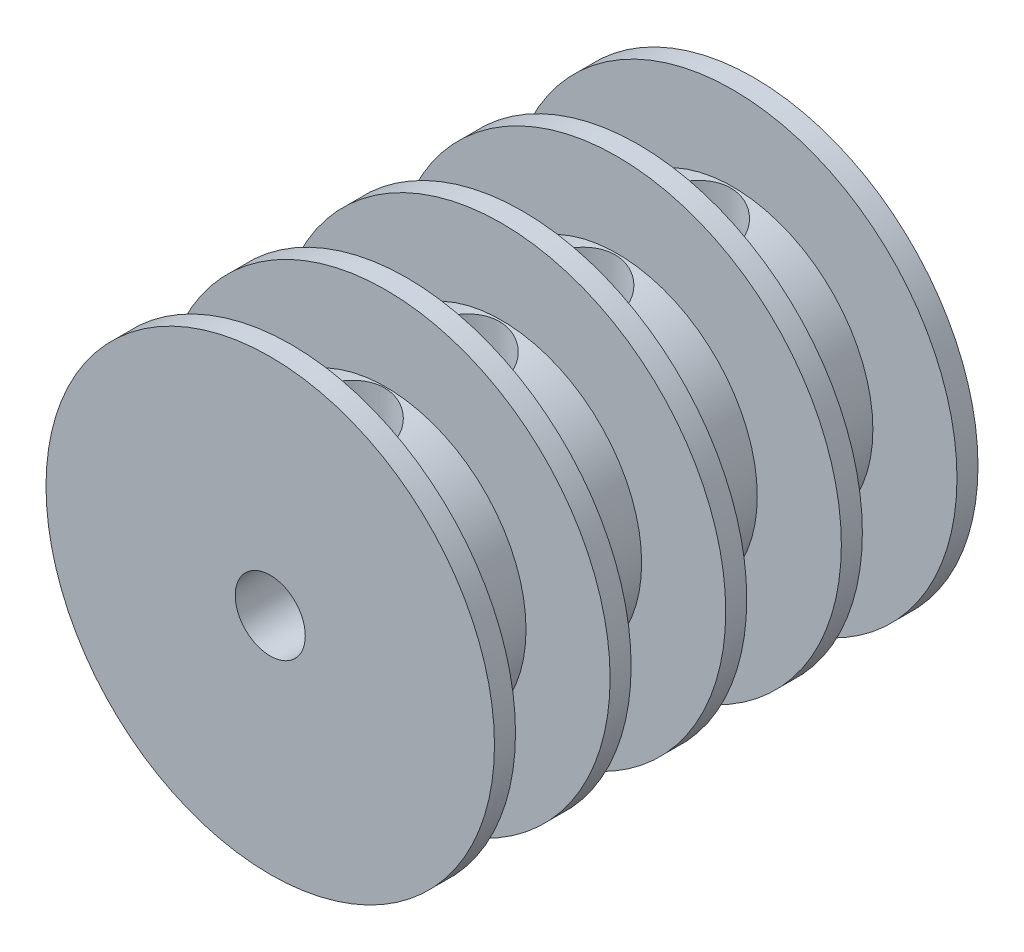
SolidWorks part; units mm, degrees
ref_plane "정면" through (0, 0, 0) normal (0, 0, 1) x (1, 0, 0)
ref_plane "윗면" through (0, 0, 0) normal (0, 1, 0) x (1, 0, 0)
ref_plane "우측면" through (0, 0, 0) normal (1, 0, 0) x (0, 0, -1)
sketch "스케치1" plane through (0, 0, 0) normal (0, 0, 1) x (1, 0, 0)
  circle A0 centre (0, 0) radius 16
  dimension "D1" = 32
extrude "보스-돌출1" add sketch "스케치1" along normal blind 1.5
sketch "스케치2" plane through (0, 0, 1.5) normal (0, 0, 1) x (1, 0, 0)
  circle A0 centre (0, 0) radius 10
  dimension "D1" = 20
extrude "보스-돌출2" add sketch "스케치2" along normal blind 15
sketch "스케치3" plane through (0, 0, 16.5) normal (0, 0, 1) x (1, 0, 0)
  circle A0 centre (0, 0) radius 16
  circle A1 centre (0, 0) radius 16 construction
extrude "보스-돌출3" add sketch "스케치3" along normal blind 1.5
ref_plane "평면2" through (0, 16, 0) normal (0, 1, 0) x (1, 0, 0)
sketch "스케치4" plane through (0, 25, 0) normal (0, 0, 1) x (-1, 0, 0)
  circle A0 centre (0, 25) radius 2.5
  dimension "D1" = 5
extrude "컷-돌출1" cut sketch "스케치4" along normal through all
hole_wizard "M3 여유 구멍1" positions "스케치7" profile "스케치6" hole size "M3" standard "ISO"
sketch "스케치7" plane through (0, 0, 13) normal (0, 0, 1) x (1, 0, 0)
  line L0 (0, 0) -> (7.0711, 7.0711) construction
  line L2 (0, 0) -> (8.0357, 0) construction
  line L3 (0, 0) -> (0, 5.0779) construction
  circle A0 centre (0, 0) radius 10
  point P0 (-7.0711, 7.0711)
  point P2 (7.0711, 7.0711)
  point P4 (7.0711, -7.0711)
  point P6 (-7.0711, -7.0711)
  dimension "D1" = 20
  dimension "D2" = 45
sketch "스케치6" plane through (-7.0711, 7.0711, 13) normal (1, 0, 0) x (0, -1, 0)
  line L0 (0, 0) -> (0, 13)
  line L1 (0, 13) -> (1.7, 13)
  line L2 (1.7, 13) -> (1.7, 0)
  line L5 (1.7, 0) -> (0, 0)
  line L11 (0, -6.35) -> (0, 107.95) construction
  dimension "관통 구멍 지름" = 3.4
  dimension "관통 구멍 깊이" = 13
ref_plane "평면1" through (0, 0, 9) normal (0, 0, -1) x (-1, 0, 0)
sketch "스케치11" plane through (0, 0, 9) normal (0, 0, -1) x (-1, 0, 0)
  circle A0 centre (0, 0) radius 16
  circle A1 centre (0, 0) radius 10
  circle A2 centre (0, 0) radius 10 construction
  circle A3 centre (0, 0) radius 16 construction
extrude "보스-돌출4" add sketch "스케치11" against normal mid plane 1.5
hole_wizard "Ø6.5 (6.5) 지름 구멍2" positions "스케치8" profile "스케치10" hole size "Ø6.5" standard "ISO"
sketch "스케치8" plane through (0, 16, 0) normal (0, 1, 0) x (1, 0, 0)
  point P0 (0, -4.9)
  dimension "D1" = 4.9
sketch "스케치10" plane through (0, 16, 4.9) normal (1, 0, 0) x (0, 0, 1)
  line L0 (0, 0) -> (0, 11.4528)
  line L1 (0, 11.4528) -> (3.25, 9.5)
  line L2 (3.25, 9.5) -> (3.25, 0)
  line L5 (3.25, 0) -> (0, 0)
  line L10 (0, 11.4528) -> (-3.25, 9.5) construction
  line L11 (0, -6.35) -> (0, 107.95) construction
  dimension "구멍 지름" = 6.5
  dimension "구멍 깊이" = 9.5
  dimension "드릴 각도" = 118
hole_wizard "M3 나사 구멍2" positions "스케치15" profile "스케치16" tap size "M3" standard "ISO" end condition through all
sketch "스케치15" plane through (0, 16, 0) normal (0, 1, 0) x (1, 0, 0)
  point P0 (0, -4.9)
sketch "스케치16" plane through (0, 16, 4.9) normal (1, 0, 0) x (0, 0, 1)
  line L0 (0, 0) -> (0, 32)
  line L1 (0, 32) -> (1.25, 32)
  line L2 (1.25, 32) -> (1.25, 0)
  line L5 (1.25, 0) -> (0, 0)
  line L11 (0, -6.35) -> (0, 107.95) construction
  dimension "관통 탭 드릴 지름" = 2.5
  dimension "관통 탭 드릴 깊이" = 32
cosmetic thread "구멍 나사산7" parameters "D2"=3
hole_wizard "Ø6.5 (6.5) 지름 구멍1" positions "스케치14" profile "스케치13" hole size "Ø6.5" standard "ISO"
sketch "스케치14" plane through (0, 16, 0) normal (0, 1, 0) x (1, 0, 0)
  line L0 (15, -9) -> (10.9672, -9) construction
  point P0 (0, -13.1)
sketch "스케치13" plane through (0, 16, 13.1) normal (1, 0, 0) x (0, 0, 1)
  line L0 (0, 0) -> (0, 11.4528)
  line L1 (0, 11.4528) -> (3.25, 9.5)
  line L2 (3.25, 9.5) -> (3.25, 0)
  line L5 (3.25, 0) -> (0, 0)
  line L10 (0, 11.4528) -> (-3.25, 9.5) construction
  line L11 (0, -6.35) -> (0, 107.95) construction
  dimension "구멍 지름" = 6.5
  dimension "구멍 깊이" = 9.5
  dimension "드릴 각도" = 118
pattern_circular "원형 패턴2" count 2 over 360 about axis through (0, 0, 0) along (0, 0, 1) of "Ø6.5 (6.5) 지름 구멍1"
hole_wizard "M3 나사 구멍3" positions "스케치17" profile "스케치18" tap size "M3" standard "ISO" end condition through all
sketch "스케치17" plane through (0, 16, 0) normal (0, 1, 0) x (1, 0, 0)
  point P0 (0, -13.1)
sketch "스케치18" plane through (0, 16, 13.1) normal (1, 0, 0) x (0, 0, 1)
  line L0 (0, 0) -> (0, 32)
  line L1 (0, 32) -> (1.25, 32)
  line L2 (1.25, 32) -> (1.25, 0)
  line L5 (1.25, 0) -> (0, 0)
  line L11 (0, -6.35) -> (0, 107.95) construction
  dimension "관통 탭 드릴 지름" = 2.5
  dimension "관통 탭 드릴 깊이" = 32
cosmetic thread "구멍 나사산10" parameters "D2"=3
sketch "스케치21" plane through (0, 0, 0) normal (0, 0, -1) x (-1, 0, 0)
  circle A0 centre (0, 0) radius 10
  circle A1 centre (0, 0) radius 10 construction
extrude "보스-돌출7" add sketch "스케치21" along normal blind 15
sketch "스케치22" plane through (0, 0, -15) normal (0, 0, -1) x (-1, 0, 0)
  circle A0 centre (0, 0) radius 16
  dimension "D1" = 32
extrude "보스-돌출8" add sketch "스케치22" along normal blind 1.5
ref_plane "평면3" through (0, 0, -7.5) normal (0, 0, -1) x (-1, 0, 0)
sketch "스케치23" plane through (0, 0, -7.5) normal (0, 0, -1) x (-1, 0, 0)
  circle A0 centre (0, 0) radius 16
  dimension "D1" = 32
extrude "보스-돌출9" add sketch "스케치23" along normal mid plane 1.5
pattern_linear "선형 패턴1" count 3 spacing 8.25 along (0, 0, -1) of "Ø6.5 (6.5) 지름 구멍2"
pattern_circular "원형 패턴1" count 2 over 360 about axis through (0, 0, 16.5) along (0, 0, -1) of "Ø6.5 (6.5) 지름 구멍2", "선형 패턴1"
hole_wizard "M3 나사 구멍4" positions "스케치24" profile "스케치25" tap size "M3" standard "ISO" end condition through all
sketch "스케치24" plane through (0, 16, 0) normal (0, 1, 0) x (1, 0, 0)
  point P0 (0, 3.35)
  point P3 (0, 11.6)
sketch "스케치25" plane through (0, 16, -3.35) normal (1, 0, 0) x (0, 0, 1)
  line L0 (0, 0) -> (0, 32)
  line L1 (0, 32) -> (1.25, 32)
  line L2 (1.25, 32) -> (1.25, 0)
  line L5 (1.25, 0) -> (0, 0)
  line L11 (0, -6.35) -> (0, 107.95) construction
  dimension "관통 탭 드릴 지름" = 2.5
  dimension "관통 탭 드릴 깊이" = 32
cosmetic thread "구멍 나사산11" parameters "D2"=3
cosmetic thread "구멍 나사산12" parameters "D2"=3
sketch "스케치26" plane through (0, 0, 18) normal (0, 0, 1) x (1, 0, 0)
  circle A0 centre (0, 0) radius 2.5
  dimension "D1" = 5
extrude "컷-돌출2" cut sketch "스케치26" against normal through all
